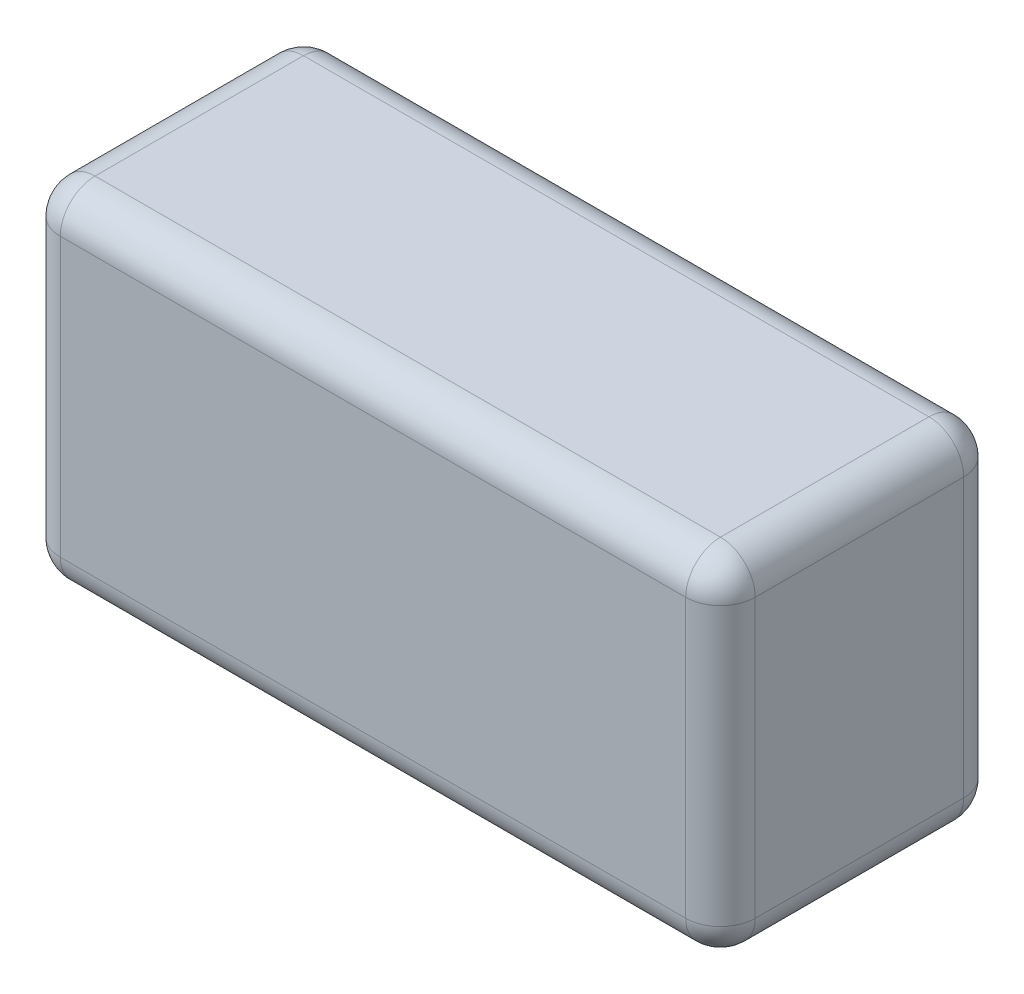
SolidWorks part; units mm, degrees
ref_plane "Front Plane" through (0, 0, 0) normal (0, 0, 1) x (1, 0, 0)
ref_plane "Top Plane" through (0, 0, 0) normal (0, 1, 0) x (1, 0, 0)
ref_plane "Right Plane" through (0, 0, 0) normal (1, 0, 0) x (0, 0, -1)
sketch "Sketch1" plane through (0, 0, 0) normal (0, 0, 1) x (1, 0, 0)
  line L1 (-31.75, -15.875) -> (31.75, -15.875)
  line L2 (-31.75, -15.875) -> (-31.75, 15.875)
  line L3 (-31.75, 15.875) -> (31.75, 15.875)
  line L4 (31.75, -15.875) -> (31.75, 15.875)
  line L5 (-31.75, -15.875) -> (31.75, 15.875) construction
  line L6 (-31.75, 15.875) -> (31.75, -15.875) construction
  point P0 (0, 0)
  dimension "D1" = 31.75
  dimension "D2" = 63.5
extrude "Boss-Extrude1" add sketch "Sketch1" along normal blind 25.4
fillet "Fillet1" radius 3.175 12 edges at (31.75, 15.875, 12.7) (-31.75, 15.875, 12.7) (-31.75, -15.875, 12.7) (31.75, -15.875, 12.7) (0, -15.875, 25.4) (-31.75, 0, 25.4) (0, 15.875, 25.4) (31.75, 0, 25.4) (0, -15.875, 0) (-31.75, 0, 0) (0, 15.875, 0) (31.75, 0, 0)
